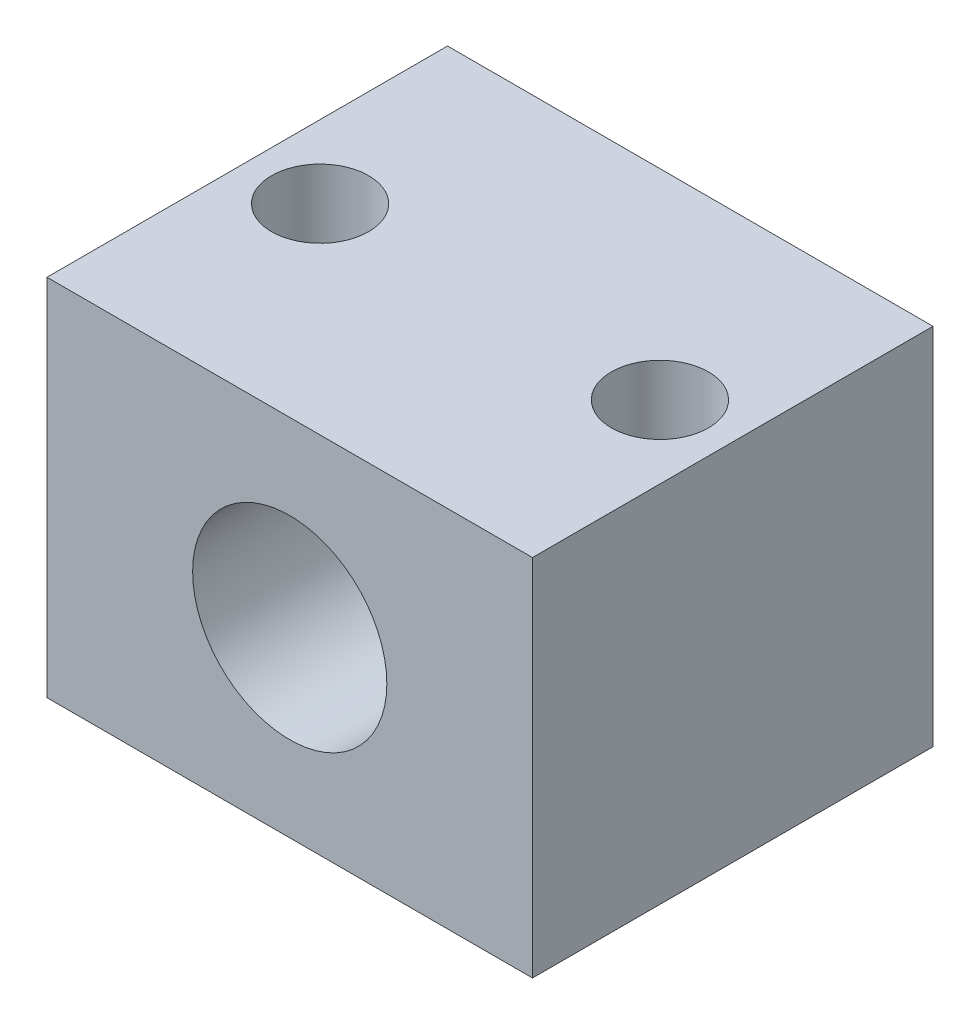
SolidWorks part; units mm, degrees
ref_plane "Plan de face" through (0, 0, 0) normal (0, 0, 1) x (1, 0, 0)
ref_plane "Plan de dessus" through (0, 0, 0) normal (0, 1, 0) x (1, 0, 0)
ref_plane "Plan de droite" through (0, 0, 0) normal (1, 0, 0) x (0, 0, -1)
sketch "Esquisse1" plane through (0, 0, 0) normal (0, 0, 1) x (1, 0, 0)
  line L0 (0, -15) -> (0, 0)
  line L1 (0, 0) -> (-20, 0)
  line L2 (-20, 0) -> (-20, -15)
  line L3 (-20, -15) -> (0, -15)
  line L4 (-20, 0) -> (0, -15) construction
  circle A0 centre (-10, -7.5) radius 4
extrude "Extrusion1" add sketch "Esquisse1" along normal blind 16.5
sketch "Esquisse2" plane through (0, 0, 0) normal (0, 1, 0) x (1, 0, 0)
  line L1 (-10, -16.5) -> (-10, 0) construction
  line L2 (0, -16.5) -> (-20, -16.5) construction
  line L3 (0, 0) -> (-20, 0) construction
  line L4 (0, -16.5) -> (-14.3502, -16.5) construction
  circle A0 centre (-17, -8.25) radius 2
  circle A2 centre (-3, -8.25) radius 2
  dimension "D1" = 8.25
extrude "Extrusion3" cut sketch "Esquisse2" against normal through all
